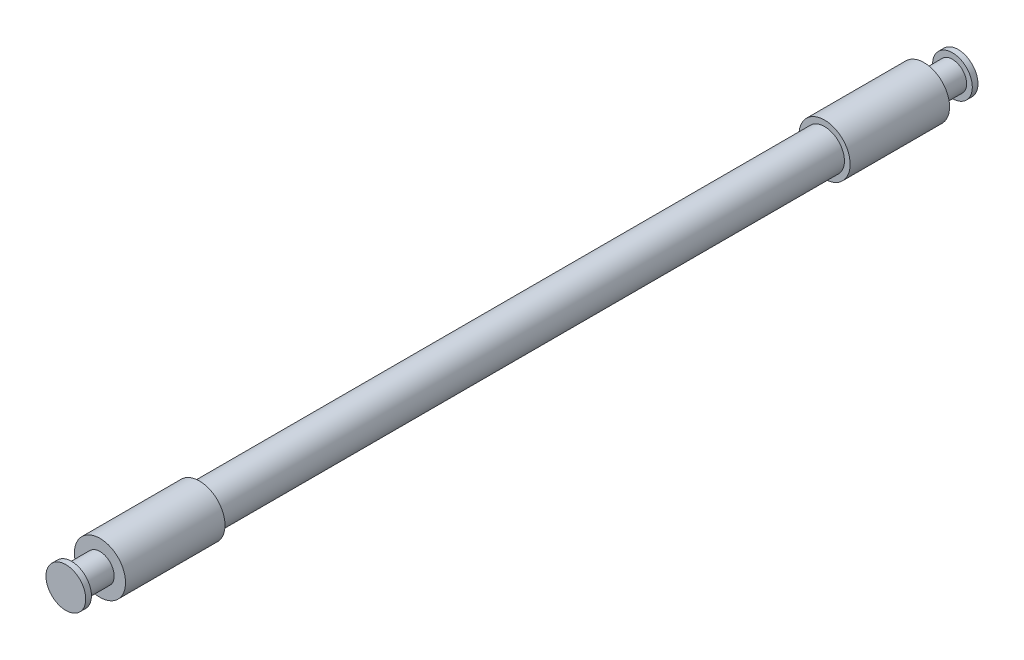
SolidWorks part; units mm, degrees
material "1060 Alloy"
ref_plane "Front Plane" through (0, 0, 0) normal (0, 0, 1) x (1, 0, 0)
ref_plane "Top Plane" through (0, 0, 0) normal (0, 1, 0) x (1, 0, 0)
ref_plane "Right Plane" through (0, 0, 0) normal (1, 0, 0) x (0, 0, -1)
sketch "Sketch1" plane through (0, 0, 0) normal (0, 1, 0) x (1, 0, 0)
  line L0 (0, 0) -> (8.89, 0) construction
  line L1 (0, 199.39) -> (0, -199.39) construction
  line L2 (0, -199.39) -> (8.89, -199.39)
  line L3 (8.89, -199.39) -> (8.89, -196.85)
  line L4 (8.89, -196.85) -> (6.35, -196.85)
  line L5 (6.35, -196.85) -> (6.35, -184.15)
  line L8 (0, -199.39) -> (0, 199.39)
  line L9 (0, 0) -> (8.89, 0) construction
  line L15 (8.89, -139.7) -> (11.43, -139.7)
  line L16 (11.43, -139.7) -> (11.43, -184.15)
  line L17 (11.43, -184.15) -> (6.35, -184.15)
  line L18 (8.89, 139.7) -> (8.89, -139.7)
  line L19 (0, 199.39) -> (8.89, 199.39)
  line L20 (8.89, 199.39) -> (8.89, 196.85)
  line L21 (8.89, 196.85) -> (6.35, 196.85)
  line L22 (6.35, 196.85) -> (6.35, 184.15)
  line L23 (11.43, 184.15) -> (6.35, 184.15)
  line L24 (11.43, 139.7) -> (11.43, 184.15)
  line L25 (8.89, 139.7) -> (11.43, 139.7)
  point P6 (6.35, -190.5)
  point P9 (0, 0)
  point P10 (4.445, 0)
  dimension "D1" = 12.7
  dimension "D2" = 2.54
  dimension "D3" = 190.5
  dimension "D4" = 12.7
  dimension "D5" = 2.54
  dimension "D6" = 2.54
  dimension "D7" = 279.4
revolve "Revolve2" add sketch "Sketch1" angle 360 about L8
